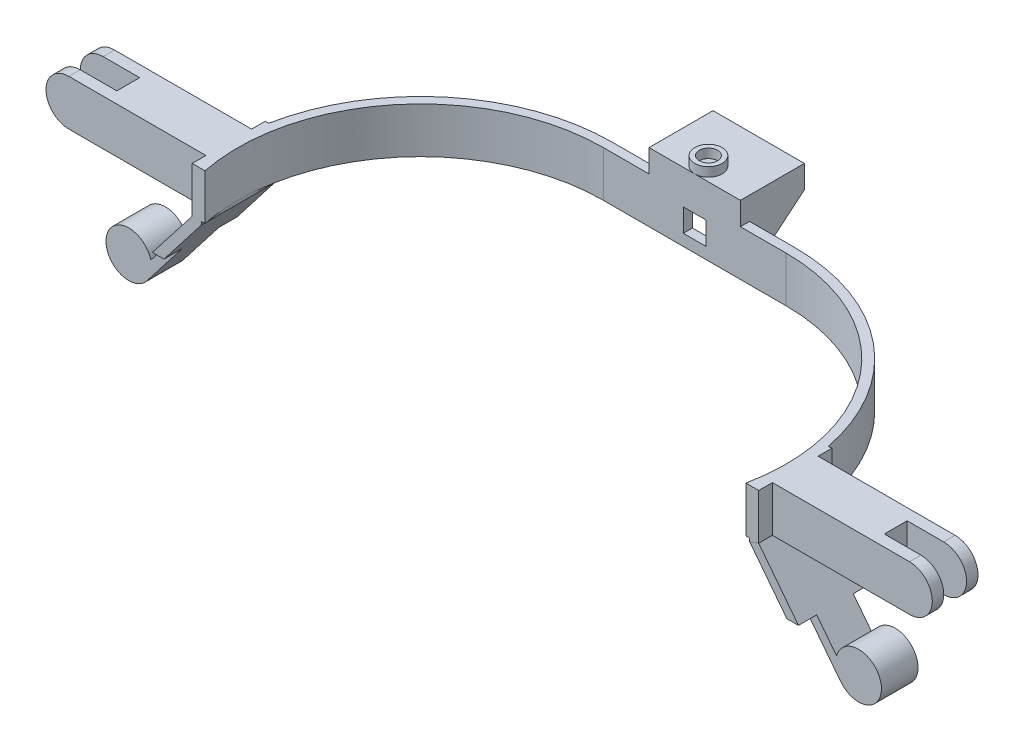
SolidWorks part; units mm, degrees
ref_plane "Front" through (0, 0, 0) normal (0, 0, 1) x (1, 0, 0)
ref_plane "Top" through (0, 0, 0) normal (0, 1, 0) x (1, 0, 0)
ref_plane "Right" through (0, 0, 0) normal (1, 0, 0) x (0, 0, -1)
sketch "草图2" plane through (0, 0, 0) normal (0, 1, 0) x (1, 0, 0)
  line L0 (-40, 0) -> (40, 0) construction
  line L1 (-40, 80) -> (40, 80)
  line L2 (-40, -80) -> (40, -80)
  line L3 (-40, 0) -> (40, 0) construction
  line L4 (-40, 84) -> (40, 84)
  line L5 (-40, -84) -> (40, -84)
  arc A0 (-40, 80) -> (-40, -80) centre (-40, 0) ccw
  arc A1 (40, -80) -> (40, 80) centre (40, 0) ccw
  arc A2 (-40, 84) -> (-40, -84) centre (-40, 0) ccw
  arc A3 (40, -84) -> (40, 84) centre (40, 0) ccw
  point P2 (0, 0)
  point P10 (0, 0)
extrude "凸台-拉伸1" add sketch "草图2" along normal blind 20
sketch "草图8" plane through (0, 20, 0) normal (0, 1, 0) x (1, 0, 0)
  line L0 (0, 0) -> (-175.2062, 0) construction
  line L1 (-124, 16) -> (-120, 16)
  line L2 (-124, 16) -> (-124, -16)
  line L3 (-124, -16) -> (-120, -16)
  line L4 (-120, 16) -> (-120, -16)
  dimension "D1" = 4
  dimension "D2" = 32
  dimension "D3" = 16
sketch "草图9" plane through (0, 0, 0) normal (0, 0, 1) x (1, 0, 0)
  line L0 (0, 0) -> (-176.3582, 0) construction
  line L1 (-155, -40) -> (155, -40) construction
  line L2 (0, 0) -> (0, -149.7853) construction
  line L3 (-124, 20) -> (-124, 0)
  line L4 (-124, 0) -> (-155, -40)
  point P11 (155, -40)
  dimension "D1" = 40
  dimension "D2" = 310
  dimension "D3" = 155
sketch "草图11" plane through (0, 20, 0) normal (0, 1, 0) x (1, 0, 0)
  line L0 (0, 0) -> (130.9327, 0) construction
  line L1 (0, 0) -> (0, 51.5924) construction
  line L3 (124, 16) -> (120, 16)
  line L4 (124, 16) -> (124, -16)
  line L5 (124, -16) -> (120, -16)
  line L6 (120, 16) -> (120, -16)
  dimension "D1" = 124
  dimension "D2" = 4
  dimension "D3" = 32
  dimension "D4" = 16
sketch "草图18" plane through (0, 0, -84) normal (0, 0, -1) x (-1, 0, 0)
  line L6 (-5, 5) -> (5, 5) construction
  line L7 (-5, 15) -> (5, 15)
  line L8 (-5, 15) -> (-5, 5)
  line L9 (-5, 5) -> (5, 5)
  line L10 (5, 15) -> (5, 5)
  dimension "D1" = 10
  dimension "D2" = 5
  dimension "D3" = 5
  dimension "D4" = 10
extrude "切除-拉伸6" cut sketch "草图18" against normal blind 10
sketch "草图20" plane through (0, 20, 0) normal (0, 1, 0) x (1, 0, 0)
  line L0 (0, 80) -> (0, 120.4936) construction
  line L1 (40, 80) -> (-40, 80) construction
  line L2 (40, 84) -> (-40, 84) construction
  line L3 (-20, 84) -> (20, 84)
  line L4 (-20, 84) -> (-20, 80)
  line L5 (-20, 80) -> (20, 80)
  line L6 (20, 84) -> (20, 80)
  dimension "D1" = 40
  dimension "D2" = 20
extrude "凸台-拉伸5" add sketch "草图20" along normal blind 10
sweep "扫描1" add profiles "草图8" path "草图9"
sketch "草图25" plane through (0, 20, 0) normal (0, 1, 0) x (1, 0, 0)
  line L1 (-122.4621, -16) -> (124.4416, -16)
  line L2 (-122.4621, -16) -> (-122.4621, -91.0614)
  line L3 (-122.4621, -91.0614) -> (124.4416, -91.0614)
  line L4 (124.4416, -16) -> (124.4416, -91.0614)
extrude "切除-拉伸7" cut sketch "草图25" against normal blind 30
sketch "草图26" plane through (-124, 0, 0) normal (-1, 0, 0) x (0, 0, 1)
  line L0 (0, 0) -> (0, 49.4965) construction
  line L1 (16, 0) -> (-16, 0) construction
  line L2 (-16, 20) -> (16, 20) construction
  line L3 (-10, 20) -> (10, 20)
  line L4 (-10, 20) -> (-10, 0)
  line L5 (-10, 0) -> (10, 0)
  line L6 (10, 20) -> (10, 0)
  dimension "D1" = 20
  dimension "D2" = 10
sketch "草图27" plane through (0, 0, 0) normal (0, 0, 1) x (1, 0, 0)
  line L0 (124, 20) -> (124, 0)
  line L1 (0, 0) -> (0, -70.6099) construction
  line L2 (124, 0) -> (155, -40)
  point P4 (-155, -40)
  point P9 (155, -40)
sweep "扫描2" add profiles "草图11" path "草图27"
extrude "凸台-拉伸6" add sketch "草图26" along normal blind 70
sketch "草图28" plane through (124, 0, 0) normal (1, 0, 0) x (0, 0, -1)
  line L0 (0, 0) -> (0, 32.1211) construction
  line L1 (-16, 20) -> (16, 20) construction
  line L2 (-10, 20) -> (10, 20)
  line L3 (-10, 20) -> (-10, 0)
  line L4 (-10, 0) -> (10, 0)
  line L5 (10, 20) -> (10, 0)
  line L6 (16, 0) -> (-16, 0) construction
  dimension "D1" = 20
  dimension "D2" = 10
extrude "凸台-拉伸7" add sketch "草图28" along normal blind 70
sketch "草图29" plane through (0, 20, 0) normal (0, 1, 0) x (1, 0, 0)
  line L0 (-194, 0) -> (194, 0) construction
  line L1 (-194, -10) -> (-194, 10) construction
  line L2 (194, 10) -> (194, -10) construction
  line L4 (-194, 5) -> (-168, 5)
  line L5 (-194, 5) -> (-194, -5)
  line L6 (-194, -5) -> (-168, -5)
  line L7 (-168, 5) -> (-168, -5)
  line L8 (194, 5) -> (168, 5)
  line L9 (194, 5) -> (194, -5)
  line L10 (194, -5) -> (168, -5)
  line L11 (168, 5) -> (168, -5)
  dimension "D1" = 10
  dimension "D2" = 26
  dimension "D3" = 5
  dimension "D4" = 5
  dimension "D5" = 10
  dimension "D6" = 26
extrude "切除-拉伸8" cut sketch "草图29" against normal blind 20
sketch "草图31" plane through (0, 0, 16) normal (0, 0, 1) x (1, 0, 0)
  line L0 (-133.6037, -18.9217) -> (-151.8383, -42.4503) construction
  line L1 (-120, -1.3686) -> (-151.8383, -42.4503) construction
  line L2 (-151.8383, -42.4503) -> (-187.4708, -14.8352) construction
  line L3 (139.7463, -26.8477) -> (151.8383, -42.4503) construction
  line L4 (120, -1.3686) -> (151.8383, -42.4503) construction
  line L5 (151.8383, -42.4503) -> (173.4376, -25.7109) construction
  circle A0 centre (-159.7425, -36.3246) radius 10
  circle A1 centre (159.7425, -36.3246) radius 10
extrude "切除-拉伸10" cut sketch "草图31" against normal through all
sketch "草图32" plane through (0, 0, 0) normal (0, 0, 1) x (1, 0, 0)
  circle A0 centre (-159.7425, -36.3246) radius 10
  circle A1 centre (159.7425, -36.3246) radius 10
extrude "凸台-拉伸8" add sketch "草图32" along normal mid plane 16
sketch "草图33" plane through (0, 0, 10) normal (0, 0, 1) x (1, 0, 0)
  line L1 (-184, 20) -> (-199.3887, 20)
  line L3 (-184, 0) -> (-199.3887, 0)
  line L4 (-199.3887, 20) -> (-199.3887, 0)
  line L5 (184, 20) -> (198.4135, 20)
  line L7 (184, 0) -> (198.4135, 0)
  line L8 (198.4135, 20) -> (198.4135, 0)
  arc A0 (-184, 20) -> (-184, 0) centre (-184, 10) ccw
  arc A1 (184, 0) -> (184, 20) centre (184, 10) ccw
extrude "切除-拉伸11" cut sketch "草图33" against normal through all
sketch "草图34" plane through (0, 0, -84) normal (0, 0, -1) x (-1, 0, 0)
  line L0 (-40, 0) -> (40, 0) construction
  line L1 (20, 30) -> (-20, 30)
  line L2 (20, 30) -> (20, 20)
  line L3 (12, 20) -> (-12, 20)
  line L4 (-20, 30) -> (-20, 20)
  line L6 (20, 20) -> (20, 0)
  line L7 (20, 0) -> (12, 0)
  line L8 (12, 20) -> (12, 0)
  line L11 (-20, 20) -> (-20, 0)
  line L12 (-20, 0) -> (-12, 0)
  line L13 (-12, 20) -> (-12, 0)
  dimension "D1" = 8
  dimension "D2" = 8
extrude "凸台-拉伸9" add sketch "草图34" along normal blind 24
sketch "草图35" plane through (20, 0, 0) normal (1, 0, 0) x (0, 0, -1)
  line L0 (108, 20) -> (84, 0)
  line L1 (108, 30) -> (108, 0) construction
  line L2 (84, 0) -> (110.8052, 0)
  line L3 (110.8052, 0) -> (108, 20)
  dimension "D1" = 10
extrude "切除-拉伸12" cut sketch "草图35" against normal through all
sketch "草图36" plane through (0, 30, 0) normal (0, 1, 0) x (1, 0, 0)
  line L0 (-20, 80) -> (20, 80) construction
  circle A0 centre (0, 86) radius 4
  circle A1 centre (0, 86) radius 6
  dimension "D1" = 6
extrude "凸台-拉伸10" add sketch "草图36" along normal blind 4
sketch "草图38" plane through (0, 0, 0) normal (1, 0, 0) x (0, 0, -1)
  line L0 (16, -42.4503) -> (8, -42.4503) construction
  line L1 (-18.5042, -22.4503) -> (-8, -22.4503)
  line L2 (-18.5042, -22.4503) -> (-18.5042, -46.3246)
  line L3 (-18.5042, -46.3246) -> (-8, -46.3246)
  line L4 (-8, -22.4503) -> (-8, -46.3246)
  line L5 (8, -46.3246) -> (19.7021, -46.3246)
  line L6 (8, -46.3246) -> (8, -22.4503)
  line L7 (8, -22.4503) -> (19.7021, -22.4503)
  line L8 (19.7021, -46.3246) -> (19.7021, -22.4503)
  line L9 (-8, -42.4503) -> (-16, -42.4503) construction
  dimension "D1" = 20
  dimension "D2" = 20
extrude "切除-拉伸13" cut sketch "草图38" against normal through all both and the other way through all
